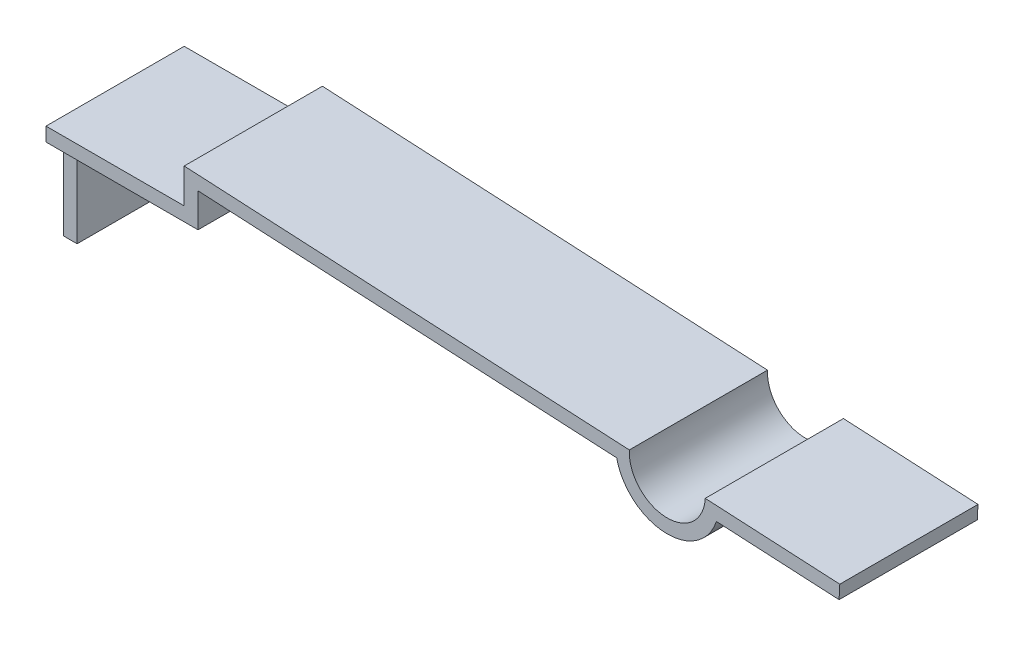
SolidWorks part; units mm, degrees
ref_plane "Front" through (0, 0, 0) normal (0, 0, 1) x (1, 0, 0)
ref_plane "Top" through (0, 0, 0) normal (0, 1, 0) x (1, 0, 0)
ref_plane "Right" through (0, 0, 0) normal (1, 0, 0) x (0, 0, -1)
sketch "草图1" plane through (0, 0, 0) normal (0, 0, 1) x (1, 0, 0)
  line L0 (0, 0) -> (0, 0.5)
  line L1 (0, 0.5) -> (6.4412, 0.1624)
  line L2 (0, 0) -> (-2, 0)
  line L3 (-2, 0) -> (-2, -1.5)
  line L4 (7.5397, 0.1049) -> (9.487, 0.0028)
  line L5 (7.7018, -0.1039) -> (9.4765, -0.1969)
  line L6 (0.2, 0.2892) -> (6.2581, -0.0282)
  line L7 (0.2, -0.2) -> (0.2, 0.2892)
  line L8 (0.2, -0.2) -> (-1.8, -0.2)
  line L9 (-1.8, -0.2) -> (-1.8, -1.5)
  line L10 (-2, -1.5) -> (-1.8, -1.5)
  line L11 (9.487, 0.0028) -> (9.4765, -0.1969)
  arc A0 (6.4412, 0.1624) -> (7.5397, 0.1049) centre (6.9904, 0.1336) ccw
  arc A1 (6.2581, -0.0282) -> (7.7018, -0.1039) centre (6.9904, 0.1336) ccw
  dimension "D4" = 87
  dimension "D1" = 1.5
  dimension "D5" = 1.1
  dimension "D2" = 2
  dimension "D3" = 0.5
  dimension "D6" = 9.5
  dimension "D7" = 7
  dimension "D8" = 0.2
extrude "凸台-拉伸1" add sketch "草图1" along normal blind 2
sketch "草图3" plane through (-1.8, 0, 0) normal (1, 0, 0) x (0, 0, -1)
  line L1 (-2, -0.2) -> (0, -0.2) construction
  line L2 (-2, -1.5) -> (-1.75, -1.5)
  line L3 (-2, -1.5) -> (-2, -0.2)
  line L4 (-2, -0.2) -> (-1.75, -0.2)
  line L5 (-1.75, -1.5) -> (-1.75, -0.2)
  line L7 (0, -1.5) -> (-0.25, -1.5)
  line L8 (0, -1.5) -> (0, -0.2)
  line L9 (0, -0.2) -> (-0.25, -0.2)
  line L10 (-0.25, -1.5) -> (-0.25, -0.2)
  dimension "D1" = 0.25
  dimension "D2" = 0.25
extrude "切除-拉伸2" cut sketch "草图3" against normal through all
